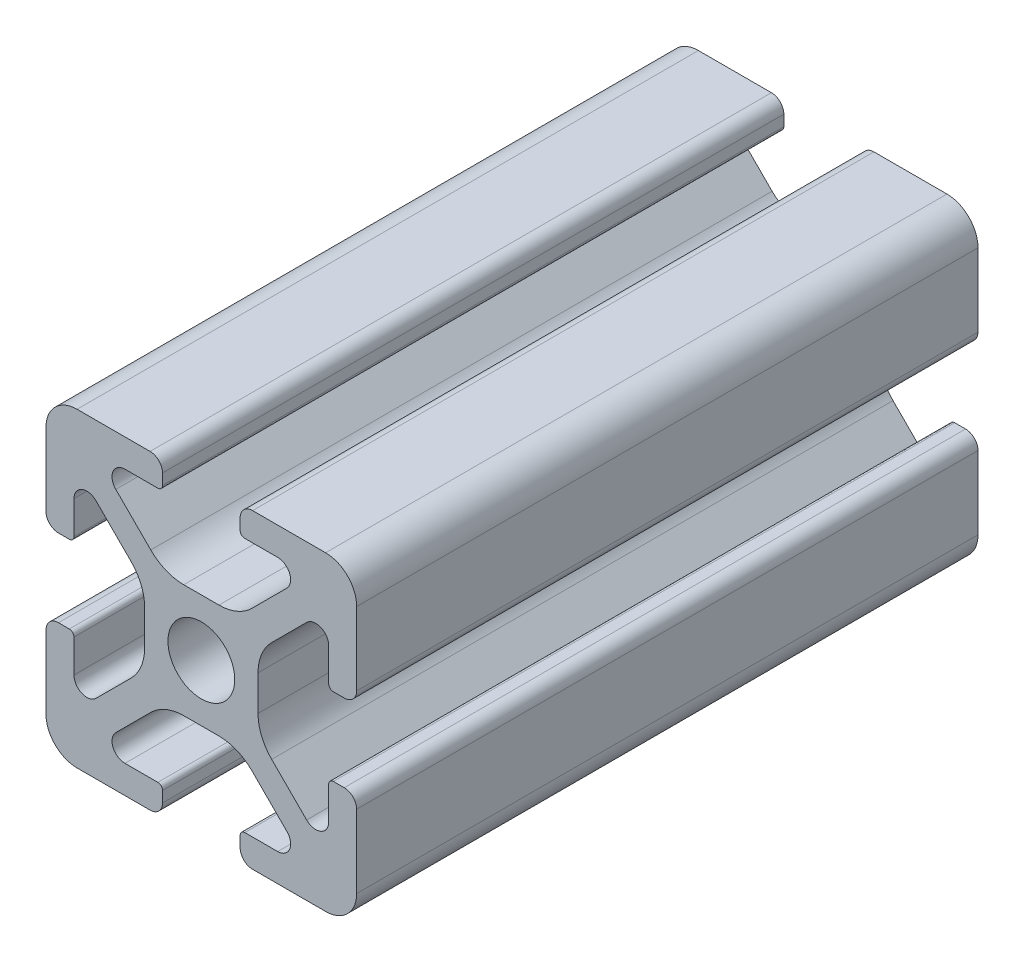
SolidWorks part; units mm, degrees
ref_plane "Front Plane" through (0, 0, 0) normal (0, 0, 1) x (1, 0, 0)
ref_plane "Top Plane" through (0, 0, 0) normal (0, 1, 0) x (1, 0, 0)
ref_plane "Right Plane" through (0, 0, 0) normal (1, 0, 0) x (0, 0, -1)
ref_plane "Plane1" through (0, 0, 0) normal (0, 0, -1) x (-1, 0, 0)
sketch "Sketch1" plane through (0, 0, 0) normal (0, 0, -1) x (-1, 0, 0)
  line L0 (-12.5, 0.8) -> (-12.5, 1.5)
  line L1 (-12.8, 1.8) -> (-14.9176, 1.8)
  line L2 (-15.5062, 3.221) -> (-13.2559, 5.4713)
  line L3 (-11.1346, 6.35) -> (-8.8654, 6.35)
  line L4 (-6.7441, 5.4713) -> (-4.4938, 3.221)
  line L5 (-5.0824, 1.8) -> (-7.2, 1.8)
  line L6 (-7.5, 1.5) -> (-7.5, 0.8)
  line L7 (-6.7, 0) -> (-2, 0)
  line L8 (0, 2) -> (0, 6.7)
  line L9 (-0.8, 7.5) -> (-1.5, 7.5)
  line L10 (-1.8, 7.2) -> (-1.8, 5.0824)
  line L11 (-3.221, 4.4938) -> (-5.4713, 6.7441)
  line L12 (-6.35, 8.8654) -> (-6.35, 11.1346)
  line L13 (-5.4713, 13.2559) -> (-3.221, 15.5062)
  line L14 (-1.8, 14.9176) -> (-1.8, 12.8)
  line L15 (-1.5, 12.5) -> (-0.8, 12.5)
  line L16 (0, 13.3) -> (0, 18)
  line L17 (-2, 20) -> (-6.7, 20)
  line L18 (-7.5, 19.2) -> (-7.5, 18.5)
  line L19 (-7.2, 18.2) -> (-5.0824, 18.2)
  line L20 (-4.4938, 16.779) -> (-6.7441, 14.5287)
  line L21 (-8.8654, 13.65) -> (-11.1346, 13.65)
  line L22 (-13.2559, 14.5287) -> (-15.5062, 16.779)
  line L23 (-14.9176, 18.2) -> (-12.8, 18.2)
  line L24 (-12.5, 18.5) -> (-12.5, 19.2)
  line L25 (-13.3, 20) -> (-18, 20)
  line L26 (-20, 18) -> (-20, 13.3)
  line L27 (-19.2, 12.5) -> (-18.5, 12.5)
  line L28 (-18.2, 12.8) -> (-18.2, 14.9176)
  line L29 (-16.779, 15.5062) -> (-14.5287, 13.2559)
  line L30 (-13.65, 11.1346) -> (-13.65, 8.8654)
  line L31 (-14.5287, 6.7441) -> (-16.779, 4.4938)
  line L32 (-18.2, 5.0824) -> (-18.2, 7.2)
  line L33 (-18.5, 7.5) -> (-19.2, 7.5)
  line L34 (-20, 6.7) -> (-20, 2)
  line L35 (-18, 0) -> (-13.3, 0)
  arc A0 (-12.5, 1.5) -> (-12.8, 1.8) centre (-12.8, 1.5) ccw
  arc A1 (-14.9176, 1.8) -> (-15.5062, 3.221) centre (-14.9176, 2.6324) cw
  arc A2 (-13.2559, 5.4713) -> (-11.1346, 6.35) centre (-11.1346, 3.35) cw
  arc A3 (-8.8654, 6.35) -> (-6.7441, 5.4713) centre (-8.8654, 3.35) cw
  arc A4 (-4.4938, 3.221) -> (-5.0824, 1.8) centre (-5.0824, 2.6324) cw
  arc A5 (-7.2, 1.8) -> (-7.5, 1.5) centre (-7.2, 1.5) ccw
  arc A6 (-7.5, 0.8) -> (-6.7, 0) centre (-6.7, 0.8) ccw
  arc A7 (-2, 0) -> (0, 2) centre (-2, 2) ccw
  arc A8 (0, 6.7) -> (-0.8, 7.5) centre (-0.8, 6.7) ccw
  arc A9 (-1.5, 7.5) -> (-1.8, 7.2) centre (-1.5, 7.2) ccw
  arc A10 (-1.8, 5.0824) -> (-3.221, 4.4938) centre (-2.6324, 5.0824) cw
  arc A11 (-5.4713, 6.7441) -> (-6.35, 8.8654) centre (-3.35, 8.8654) cw
  arc A12 (-6.35, 11.1346) -> (-5.4713, 13.2559) centre (-3.35, 11.1346) cw
  arc A13 (-3.221, 15.5062) -> (-1.8, 14.9176) centre (-2.6324, 14.9176) cw
  arc A14 (-1.8, 12.8) -> (-1.5, 12.5) centre (-1.5, 12.8) ccw
  arc A15 (-0.8, 12.5) -> (0, 13.3) centre (-0.8, 13.3) ccw
  arc A16 (0, 18) -> (-2, 20) centre (-2, 18) ccw
  arc A17 (-6.7, 20) -> (-7.5, 19.2) centre (-6.7, 19.2) ccw
  arc A18 (-7.5, 18.5) -> (-7.2, 18.2) centre (-7.2, 18.5) ccw
  arc A19 (-5.0824, 18.2) -> (-4.4938, 16.779) centre (-5.0824, 17.3676) cw
  arc A20 (-6.7441, 14.5287) -> (-8.8654, 13.65) centre (-8.8654, 16.65) cw
  arc A21 (-11.1346, 13.65) -> (-13.2559, 14.5287) centre (-11.1346, 16.65) cw
  arc A22 (-15.5062, 16.779) -> (-14.9176, 18.2) centre (-14.9176, 17.3676) cw
  arc A23 (-12.8, 18.2) -> (-12.5, 18.5) centre (-12.8, 18.5) ccw
  arc A24 (-12.5, 19.2) -> (-13.3, 20) centre (-13.3, 19.2) ccw
  arc A25 (-18, 20) -> (-20, 18) centre (-18, 18) ccw
  arc A26 (-20, 13.3) -> (-19.2, 12.5) centre (-19.2, 13.3) ccw
  arc A27 (-18.5, 12.5) -> (-18.2, 12.8) centre (-18.5, 12.8) ccw
  arc A28 (-18.2, 14.9176) -> (-16.779, 15.5062) centre (-17.3676, 14.9176) cw
  arc A29 (-14.5287, 13.2559) -> (-13.65, 11.1346) centre (-16.65, 11.1346) cw
  arc A30 (-13.65, 8.8654) -> (-14.5287, 6.7441) centre (-16.65, 8.8654) cw
  arc A31 (-16.779, 4.4938) -> (-18.2, 5.0824) centre (-17.3676, 5.0824) cw
  arc A32 (-18.2, 7.2) -> (-18.5, 7.5) centre (-18.5, 7.2) ccw
  arc A33 (-19.2, 7.5) -> (-20, 6.7) centre (-19.2, 6.7) ccw
  arc A34 (-20, 2) -> (-18, 0) centre (-18, 2) ccw
  arc A35 (-13.3, 0) -> (-12.5, 0.8) centre (-13.3, 0.8) ccw
  circle A36 centre (-10, 10) radius 2.15
extrude "Boss-Extrude1" add sketch "Sketch1" against normal blind 40
equation "\"plate_thickness\" = 6.35 'thickness of the plate "
equation "\"t_height\" = 200"
equation "\"t_width\" = 240"
equation "\"t_length\" = 240"
equation "\"D1@Boss-Extrude1\"=\"locomotion_height\""
equation "\"connector_D1\" = 70 'the big holes diameter"
equation "\"mtg_hole_D\" = 5.5 'mounting holes"
equation "\"mtg_dfc\" = 40 'mounting hole distance from center"
equation "\"plate_hole_from_edge\" = 9"
equation "\"plate_spacing\" = 1"
equation "\"front_plate_height\" = \"t_height\" + 38"
equation "\"front_plate_width\" = \"t_width\" + 38"
equation "\"side_plate_height\" = \"front_plate_height\""
equation "\"side_plate_length\" = \"t_length\" + 38"
equation "\"top_plate_width\" = \"front_plate_width\""
equation "\"top_plate_length\" = \"side_plate_length\""
equation "\"itx_support_t_slot_length\" = \"t_width\" + (2 * 20.5)"
equation "\"locomotion_length\" = \"t_length\""
equation "\"locomotion_width\" = \"t_width\""
equation "\"locomotion_height\" = 40"
equation "\"itx_mtg_hole_spacing\" = 40"
